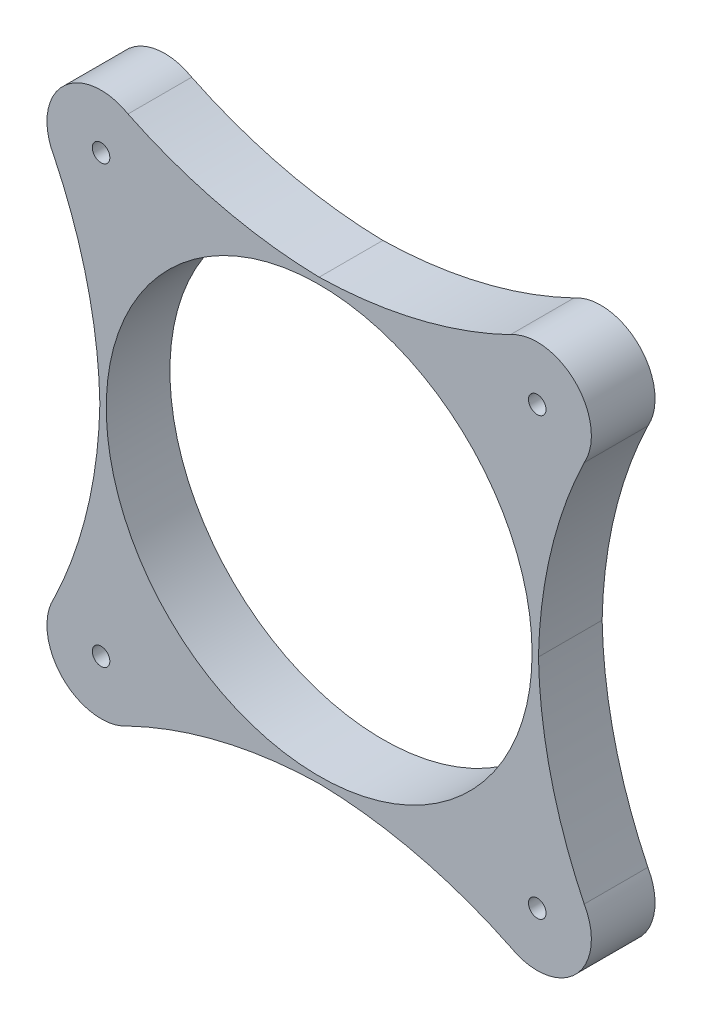
SolidWorks part; units mm, degrees
material "ABS"
ref_plane "Front Plane" through (0, 0, 0) normal (0, 0, 1) x (1, 0, 0)
ref_plane "Top Plane" through (0, 0, 0) normal (0, 1, 0) x (1, 0, 0)
ref_plane "Right Plane" through (0, 0, 0) normal (1, 0, 0) x (0, 0, -1)
sketch "Sketch1" plane through (0, 0, 0) normal (0, 0, 1) x (1, 0, 0)
  circle A0 centre (0, 0) radius 84.9312
  arc A24 (-76.246, 105.7195) -> (0, 87.4712) centre (3.7574, 271.5829) ccw
  arc A25 (0, 87.4712) -> (76.246, 105.7195) centre (-3.7574, 271.5829) ccw
  arc A26 (105.7195, 76.246) -> (76.246, 105.7195) centre (86.9962, 86.9962) ccw
  arc A27 (105.7195, 76.246) -> (87.4713, 0) centre (271.5829, -3.7574) ccw
  arc A28 (87.4713, 0) -> (105.7195, -76.246) centre (271.5829, 3.7574) ccw
  arc A29 (76.246, -105.7195) -> (105.7195, -76.246) centre (86.9962, -86.9962) ccw
  arc A30 (76.246, -105.7195) -> (0, -87.4712) centre (-3.7574, -271.5829) ccw
  arc A31 (0, -87.4712) -> (-76.246, -105.7195) centre (3.7574, -271.5829) ccw
  arc A32 (-105.7195, -76.246) -> (-76.246, -105.7195) centre (-86.9962, -86.9962) ccw
  arc A33 (-105.7195, -76.246) -> (-87.4713, 0) centre (-271.5829, 3.7574) ccw
  arc A34 (-87.4713, 0) -> (-105.7195, 76.246) centre (-271.5829, -3.7574) ccw
  arc A35 (-76.246, 105.7195) -> (-105.7195, 76.246) centre (-86.9962, 86.9962) ccw
  dimension "D2" = 169.8625
extrude "Boss-Extrude1" add sketch "Sketch1" along normal blind 25.4
hole_wizard "CBORE for M6 Hex Head Bolt1" positions "Sketch2" profile "Sketch3" counterbore size "M6" standard "ISO" end condition through all
sketch "Sketch2" plane through (0, 0, 0) normal (0, 0, -1) x (-1, 0, 0)
  point P0 (-86.9962, 86.9962)
  point P3 (86.9962, 86.9962)
  point P6 (86.9962, -86.9962)
  point P9 (-86.9962, -86.9962)
sketch "Sketch3" plane through (86.9962, 86.9962, 0) normal (1, 0, 0) x (0, 1, 0)
  line L0 (0, 0) -> (0, 25.4)
  line L1 (0, 25.4) -> (3.5, 25.4)
  line L3 (3.5, 25.4) -> (3.5, 4)
  line L4 (3.5, 4) -> (7.2735, 4)
  line L5 (7.2735, 4) -> (7.2735, 0)
  line L7 (7.2735, 0) -> (0, 0)
  line L11 (0, -6.35) -> (0, 107.95) construction
  dimension "Thru Hole Dia." = 7
  dimension "Thru Hole Depth" = 25.4
  dimension "C'Bore Dia." = 14.547
  dimension "C'Bore Depth" = 4
